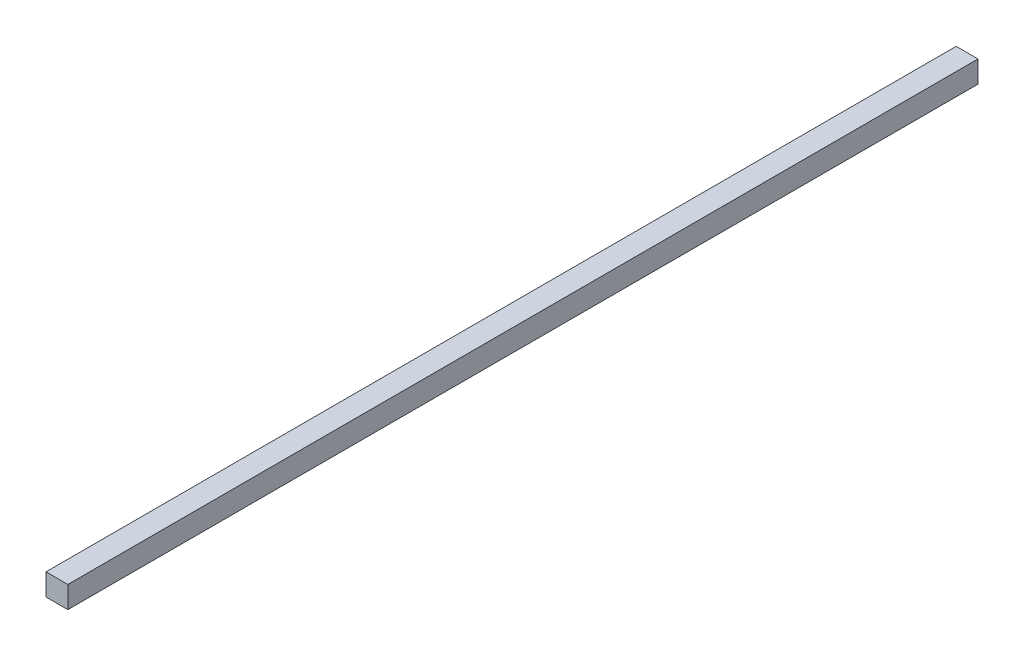
SolidWorks part; units mm, degrees
ref_plane "Face" through (0, 0, 0) normal (0, 0, 1) x (1, 0, 0)
ref_plane "Dessus" through (0, 0, 0) normal (0, 1, 0) x (1, 0, 0)
ref_plane "Droite" through (0, 0, 0) normal (1, 0, 0) x (0, 0, -1)
sketch "Esquisse1" plane through (0, 0, 0) normal (0, 0, 1) x (1, 0, 0)
  line L1 (0, 0) -> (18, 0)
  line L2 (0, 0) -> (0, 18)
  line L3 (0, 18) -> (18, 18)
  line L4 (18, 0) -> (18, 18)
  dimension "D1" = 18
  dimension "D2" = 18
extrude "Extrusion1" add sketch "Esquisse1" against normal blind 750
